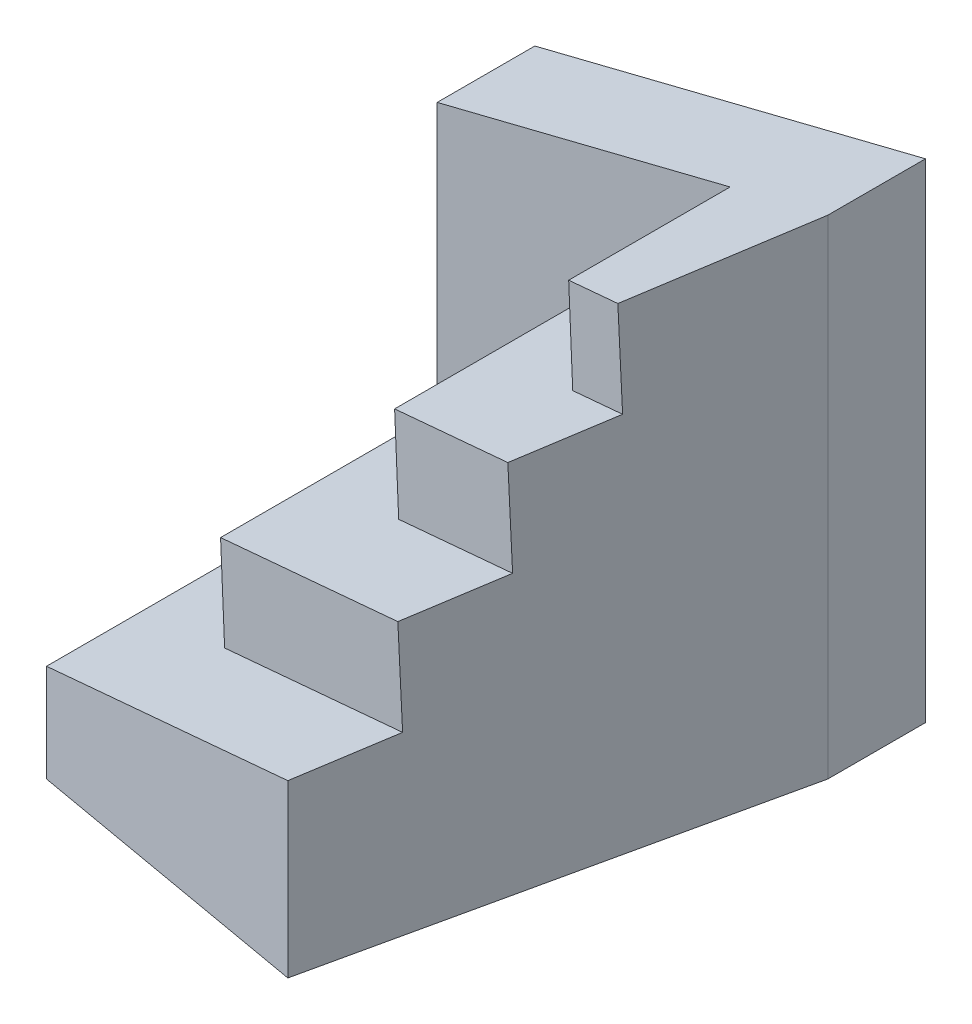
SolidWorks part; units mm, degrees
other "Perspective"
ref_plane "Front" through (0, 0, 0) normal (0, 0, 1) x (1, 0, 0)
ref_plane "Top" through (0, 0, 0) normal (0, 1, 0) x (1, 0, 0)
ref_plane "Right" through (0, 0, 0) normal (1, 0, 0) x (0, 0, -1)
sketch "Sketch1" plane through (0, 0, 0) normal (0, 1, 0) x (1, 0, 0)
  line L0 (0, 0) -> (0, 90)
  line L1 (0, 90) -> (72, 90)
  line L2 (72, 90) -> (72, 72)
  line L3 (72, 72) -> (54, -9.5217)
  line L4 (54, -9.5217) -> (0, 0)
  dimension "D1" = 18
  dimension "D2" = 72
  dimension "D3" = 90
  dimension "D4" = 100
  dimension "D5" = 54
extrude "Main Block" add sketch "Sketch1" along normal blind 90
sketch "Sketch4" plane through (0, 0, 0) normal (0, 0, 1) x (1, 0, 0)
  line L0 (18, 40.5) -> (18, 22.5)
  line L1 (0, 90) -> (0, 18)
  line L2 (36, 63) -> (36, 45)
  line L7 (0, 18) -> (18, 22.5)
  line L10 (0, 90) -> (54, 90)
  line L11 (18, 40.5) -> (36, 45)
  line L12 (36, 63) -> (54, 67.5)
  line L15 (54, 90) -> (54, 67.5)
extrude "Main Cutout" cut sketch "Sketch4" against normal blind 72 and the other way blind 10
sketch "Sketch5" plane through (0, 0, 0) normal (0, 0, 1) x (1, 0, 0)
  line L0 (0, 90) -> (72, 90)
  line L2 (0, 72) -> (72, 90)
  line L3 (0, 90) -> (0, 72)
extrude "Top Slope Cut" cut sketch "Sketch5" against normal blind 90 and the other way blind 12
sketch "Sketch6" plane through (-4.2353, 16.9412, 0) normal (-0.2425, 0.9701, 0) x (-0.9701, -0.2425, 0)
  line L0 (-92.8922, -2.8565) -> (-85.2037, 13.8283)
  line L1 (-4.3656, 0) -> (-85.2037, 13.8283)
  line L2 (-22.9196, 3.1739) -> (-4.3656, 0) construction
  line L3 (-4.3656, -18) -> (-92.8922, -2.8565)
  line L4 (-4.3656, -72) -> (-4.3656, 0) construction
  line L5 (-4.3656, -18) -> (-4.3656, 0)
  dimension "D1" = 18
extrude "First Step Cut" cut sketch "Sketch6" along normal blind 90
sketch "Sketch7" plane through (-8.4706, 33.8824, 0) normal (-0.2425, 0.9701, 0) x (-0.9701, -0.2425, 0)
  line L0 (-27.2853, -14.0793) -> (-101.7428, -1.3424)
  line L1 (-60.0276, 9.5217) -> (-4.3656, 0) construction
  line L2 (-27.2853, -32.0793) -> (-101.7706, -19.3377)
  line L3 (-27.2853, -72) -> (-27.2853, -14.0793) construction
  line L4 (-27.2853, -32.0793) -> (-27.2853, -14.0793)
  line L5 (-101.7706, -19.3377) -> (-101.7428, -1.3424)
  dimension "D1" = 18
extrude "Second Step Cut" cut sketch "Sketch7" along normal blind 50
sketch "Sketch8" plane through (-12.7059, 50.8235, 0) normal (-0.2425, 0.9701, 0) x (-0.9701, -0.2425, 0)
  line L0 (-50.2049, -28.1586) -> (-102.9133, -19.1422)
  line L1 (-60.0276, 9.5217) -> (-4.3656, 0) construction
  line L2 (-50.2049, -46.1586) -> (-106.8275, -36.4726)
  line L3 (-50.2049, -72) -> (-50.2049, -28.1586) construction
  line L4 (-102.9133, -19.1422) -> (-106.8275, -36.4726)
  line L5 (-50.2049, -28.1586) -> (-50.2049, -46.1586)
  dimension "D1" = 18
extrude "Third Step Cut" cut sketch "Sketch8" along normal blind 20
